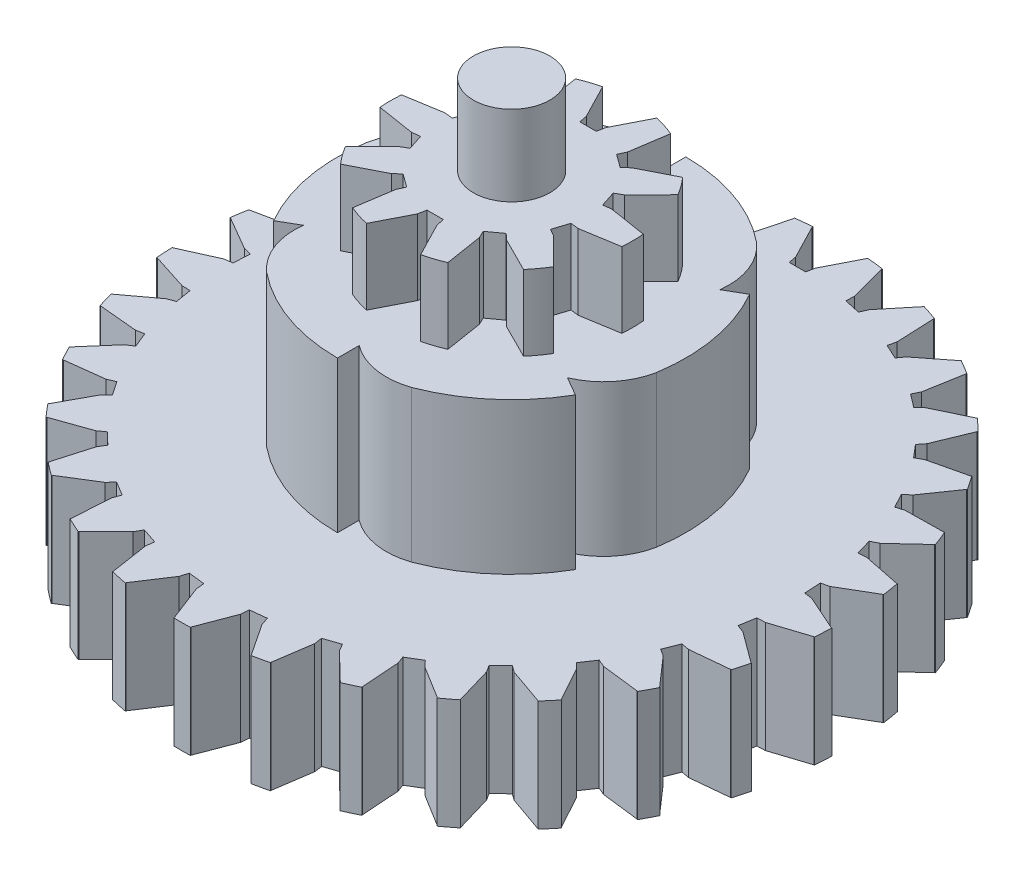
SolidWorks part; units mm, degrees
material "Gray Cast Iron"
ref_plane "Front Plane" through (0, 0, 0) normal (0, 0, 1) x (1, 0, 0)
ref_plane "Top Plane" through (0, 0, 0) normal (0, 1, 0) x (1, 0, 0)
ref_plane "Right Plane" through (0, 0, 0) normal (1, 0, 0) x (0, 0, -1)
sketch "Sketch1" plane through (0, 0, 0) normal (0, 1, 0) x (1, 0, 0)
  circle A0 centre (-83.1207, 52.7325) radius 4.5085
extrude "Boss-Extrude1" add sketch "Sketch1" along normal blind 2.794
sketch "Sketch2" plane through (0, 2.794, 0) normal (0, 1, 0) x (1, 0, 0)
  circle A0 centre (-83.1207, 52.7325) radius 1.4224
extrude "Boss-Extrude2" add sketch "Sketch2" along normal blind 2.9845
sketch "Sketch3" plane through (0, 2.794, 0) normal (0, 1, 0) x (1, 0, 0)
  line L0 (-83.1207, 55.5745) -> (-82.8159, 55.5745)
  line L1 (-83.1207, 55.5745) -> (-83.4255, 55.5745)
  line L2 (-83.4255, 55.5745) -> (-83.4853, 55.8734)
  line L3 (-82.8159, 55.5745) -> (-82.7574, 55.8745)
  line L4 (-82.7574, 55.8745) -> (-82.1099, 57.1432)
  line L5 (-83.4853, 55.8734) -> (-84.1407, 57.1427)
  line L6 (-83.1207, 52.7325) -> (-83.1207, 57.241)
  line L7 (-84.1407, 57.1427) -> (-84.2034, 57.9061)
  line L8 (-84.2034, 57.9061) -> (-82.0598, 57.9061)
  line L9 (-82.0598, 57.9061) -> (-82.1099, 57.1432)
  line L10 (-81.5695, 55.4878) -> (-81.3537, 56.8999)
  line L11 (-79.2215, 56.2944) -> (-79.7104, 55.7067)
  line L12 (-80.9799, 55.0609) -> (-79.7104, 55.7067)
  line L13 (-81.2036, 54.8526) -> (-80.9799, 55.0609)
  line L14 (-81.4502, 55.0317) -> (-81.2036, 54.8526)
  line L15 (-81.4502, 55.0317) -> (-81.6968, 55.2109)
  line L16 (-81.6968, 55.2109) -> (-81.5695, 55.4878)
  line L17 (-81.3537, 56.8999) -> (-80.9557, 57.5544)
  line L18 (-80.9557, 57.5544) -> (-79.2215, 56.2944)
  line L19 (-80.2462, 54.0498) -> (-79.2416, 55.0654)
  line L20 (-77.8725, 53.3223) -> (-78.6135, 53.1341)
  line L21 (-80.0202, 53.3579) -> (-78.6135, 53.1341)
  line L22 (-80.3236, 53.3208) -> (-80.0202, 53.3579)
  line L23 (-80.4178, 53.6107) -> (-80.3236, 53.3208)
  line L24 (-80.4178, 53.6107) -> (-80.512, 53.9006)
  line L25 (-80.512, 53.9006) -> (-80.2462, 54.0498)
  line L26 (-79.2416, 55.0654) -> (-78.5349, 55.3609)
  line L27 (-78.5349, 55.3609) -> (-77.8725, 53.3223)
  line L28 (-80.0209, 52.1086) -> (-78.6112, 52.3397)
  line L29 (-78.5282, 50.1248) -> (-79.2382, 50.4081)
  line L30 (-80.2447, 51.416) -> (-79.2382, 50.4081)
  line L31 (-80.512, 51.5644) -> (-80.2447, 51.416)
  line L32 (-80.4178, 51.8543) -> (-80.512, 51.5644)
  line L33 (-80.4178, 51.8543) -> (-80.3236, 52.1441)
  line L34 (-80.3236, 52.1441) -> (-80.0209, 52.1086)
  line L35 (-78.6112, 52.3397) -> (-77.8658, 52.1635)
  line L36 (-77.8658, 52.1635) -> (-78.5282, 50.1248)
  line L37 (-80.9796, 50.4058) -> (-79.7033, 49.7641)
  line L38 (-80.938, 47.9234) -> (-81.3459, 48.57)
  line L39 (-81.5678, 49.977) -> (-81.3459, 48.57)
  line L40 (-81.6968, 50.2541) -> (-81.5678, 49.977)
  line L41 (-81.4502, 50.4333) -> (-81.6968, 50.2541)
  line L42 (-81.4502, 50.4333) -> (-81.2036, 50.6124)
  line L43 (-81.2036, 50.6124) -> (-80.9796, 50.4058)
  line L44 (-79.7033, 49.7641) -> (-79.2038, 49.1834)
  line L45 (-79.2038, 49.1834) -> (-80.938, 47.9234)
  line L46 (-82.7561, 49.5916) -> (-82.1007, 48.3223)
  line L47 (-84.1816, 47.5589) -> (-84.1315, 48.3217)
  line L48 (-83.484, 49.5904) -> (-84.1315, 48.3217)
  line L49 (-83.4255, 49.8905) -> (-83.484, 49.5904)
  line L50 (-83.1207, 49.8905) -> (-83.4255, 49.8905)
  line L51 (-83.1207, 49.8905) -> (-82.8159, 49.8905)
  line L52 (-82.8159, 49.8905) -> (-82.7561, 49.5916)
  line L53 (-82.1007, 48.3223) -> (-82.038, 47.5589)
  line L54 (-82.038, 47.5589) -> (-84.1816, 47.5589)
  line L55 (-84.6719, 49.9772) -> (-84.8877, 48.5651)
  line L56 (-87.0199, 49.1705) -> (-86.5311, 49.7583)
  line L57 (-85.2615, 50.4041) -> (-86.5311, 49.7583)
  line L58 (-85.0378, 50.6124) -> (-85.2615, 50.4041)
  line L59 (-84.7912, 50.4333) -> (-85.0378, 50.6124)
  line L60 (-84.7912, 50.4333) -> (-84.5446, 50.2541)
  line L61 (-84.5446, 50.2541) -> (-84.6719, 49.9772)
  line L62 (-84.8877, 48.5651) -> (-85.2857, 47.9106)
  line L63 (-85.2857, 47.9106) -> (-87.0199, 49.1705)
  line L64 (-85.9952, 51.4152) -> (-86.9998, 50.3996)
  line L65 (-88.3689, 52.1427) -> (-87.6279, 52.3309)
  line L66 (-86.2212, 52.1071) -> (-87.6279, 52.3309)
  line L67 (-85.9178, 52.1441) -> (-86.2212, 52.1071)
  line L68 (-85.8236, 51.8543) -> (-85.9178, 52.1441)
  line L69 (-85.8236, 51.8543) -> (-85.7294, 51.5644)
  line L70 (-85.7294, 51.5644) -> (-85.9952, 51.4152)
  line L71 (-86.9998, 50.3996) -> (-87.7065, 50.104)
  line L72 (-87.7065, 50.104) -> (-88.3689, 52.1427)
  line L73 (-86.2205, 53.3563) -> (-87.6302, 53.1252)
  line L74 (-87.7132, 55.3402) -> (-87.0032, 55.0568)
  line L75 (-85.9967, 54.049) -> (-87.0032, 55.0568)
  line L76 (-85.7294, 53.9006) -> (-85.9967, 54.049)
  line L77 (-85.8236, 53.6107) -> (-85.7294, 53.9006)
  line L78 (-85.8236, 53.6107) -> (-85.9178, 53.3208)
  line L79 (-85.9178, 53.3208) -> (-86.2205, 53.3563)
  line L80 (-87.6302, 53.1252) -> (-88.3756, 53.3015)
  line L81 (-88.3756, 53.3015) -> (-87.7132, 55.3402)
  line L82 (-85.2618, 55.0592) -> (-86.5381, 55.7009)
  line L83 (-85.3034, 57.5416) -> (-84.8955, 56.895)
  line L84 (-84.6736, 55.488) -> (-84.8955, 56.895)
  line L85 (-84.5446, 55.2109) -> (-84.6736, 55.488)
  line L86 (-84.7912, 55.0317) -> (-84.5446, 55.2109)
  line L87 (-84.7912, 55.0317) -> (-85.0378, 54.8526)
  line L88 (-85.0378, 54.8526) -> (-85.2618, 55.0592)
  line L89 (-86.5381, 55.7009) -> (-87.0376, 56.2816)
  line L90 (-87.0376, 56.2816) -> (-85.3034, 57.5416)
  line L91 (-83.1207, 52.7325) -> (-83.1207, 55.5745) construction
  circle A0 centre (-83.1207, 52.7325) radius 4.5085 construction
  circle M11 centre (-83.1207, 52.7325) radius 4.5085
  dimension "D1" = 10
  dimension "D2" = 2.842
extrude "Cut-Extrude1" cut sketch "Sketch3" against normal through all contours L88 L87 L86 L85 L84 L82 M11 | L6 L0 L3 L4 M11 | L1 L6 L5 L2 M11 | L16 L15 L14 L13 L12 L10 M11 | L25 L24 L23 L22 L21 L19 M11 | L34 L33 L32 L31 L30 L28 M11 | L43 L42 L41 L40 L39 L37 M11 | L52 L51 L50 L49 L48 L46 M11 | L61 L60 L59 L58 L57 L55 M11 | L70 L69 L68 L67 L66 L64 M11 | L79 L78 L77 L76 L75 L73 M11
sketch "Sketch4" plane through (0, 0, 0) normal (0, -1, 0) x (1, 0, 0)
  circle A0 centre (-83.1207, -52.7325) radius 6.477
extrude "Boss-Extrude3" add sketch "Sketch4" along normal blind 5.6261
sketch "Sketch5" plane through (0, 0, 0) normal (0, 1, 0) x (1, 0, 0)
  line L0 (-83.1207, 58.4015) -> (-83.1207, 59.2095)
  line L6 (-78.2112, 55.567) -> (-77.5115, 55.971)
  line L7 (-78.2112, 49.898) -> (-77.5115, 49.494)
  line L8 (-83.1207, 47.0635) -> (-83.1207, 46.2555)
  line L9 (-88.0302, 49.898) -> (-88.7299, 49.494)
  line L10 (-88.0302, 55.567) -> (-88.7299, 55.971)
  line L11 (-83.1207, 52.7325) -> (-84.6382, 56.3955) construction
  circle A0 centre (-83.1207, 52.7325) radius 6.477 construction
  arc A2 (-83.1207, 58.4015) -> (-85.4488, 58.7766) centre (-84.6382, 56.3955) ccw
  arc A3 (-85.4488, 58.7766) -> (-83.1207, 59.2095) centre (-83.1207, 52.7325) cw
  arc A14 (-79.0504, 57.7708) -> (-77.5115, 55.971) centre (-83.1207, 52.7325) cw
  arc A15 (-78.2112, 55.567) -> (-79.0504, 57.7708) centre (-80.7072, 55.8782) ccw
  arc A16 (-76.7223, 51.7267) -> (-77.5115, 49.494) centre (-83.1207, 52.7325) cw
  arc A17 (-78.2112, 49.898) -> (-76.7223, 51.7267) centre (-79.1897, 52.2152) ccw
  arc A18 (-80.7926, 46.6884) -> (-83.1207, 46.2555) centre (-83.1207, 52.7325) cw
  arc A19 (-83.1207, 47.0635) -> (-80.7926, 46.6884) centre (-81.6032, 49.0695) ccw
  arc A20 (-87.191, 47.6942) -> (-88.7299, 49.494) centre (-83.1207, 52.7325) cw
  arc A21 (-88.0302, 49.898) -> (-87.191, 47.6942) centre (-85.5342, 49.5868) ccw
  arc A22 (-89.5191, 53.7383) -> (-88.7299, 55.971) centre (-83.1207, 52.7325) cw
  arc A23 (-88.0302, 55.567) -> (-89.5191, 53.7383) centre (-87.0517, 53.2498) ccw
  dimension "D1" = 6
  dimension "D2" = 3.9649
extrude "Cut-Extrude2" cut sketch "Sketch5" against normal through all contours L0 A3 A2 | A23 A22 L10 | A21 A20 L9 | A19 A18 L8 | A17 A16 L7 | A15 A14 L6
sketch "Sketch6" plane through (0, -5.6261, 0) normal (0, -1, 0) x (1, 0, 0)
  circle A0 centre (-83.1207, -52.7325) radius 12.2619
extrude "Boss-Extrude4" add sketch "Sketch6" along normal blind 4.1275 contours A0
sketch "Sketch7" plane through (0, -9.7536, 0) normal (0, -1, 0) x (1, 0, 0)
  circle A0 centre (-83.1207, -52.7325) radius 1.4224
extrude "Boss-Extrude5" add sketch "Sketch7" along normal blind 3.302 contours A0
ref_plane "Plane1" through (0, 0, -40.4622) normal (0, 0, 1) x (1, 0, 0)
sketch "Sketch11" plane through (0, -5.6261, 0) normal (0, 1, 0) x (1, 0, 0)
  line L0 (-83.1207, 52.7325) -> (-83.1207, 64.9943)
  line L1 (-83.1207, 63.3604) -> (-82.8159, 63.3604)
  line L2 (-83.1207, 63.3604) -> (-83.4255, 63.3604)
  line L3 (-83.4255, 63.3604) -> (-83.4853, 63.6593)
  line L4 (-82.8159, 63.3604) -> (-82.7574, 63.6604)
  line L5 (-82.7574, 63.6604) -> (-82.1099, 64.9291)
  line L6 (-83.4853, 63.6593) -> (-84.1407, 64.9286)
  line L7 (-84.1407, 64.9286) -> (-84.2034, 65.692)
  line L9 (-82.0598, 65.692) -> (-82.1099, 64.9291)
  line L10 (-84.2034, 65.692) -> (-82.0598, 65.692)
  circle A0 centre (-83.1207, 52.7325) radius 12.2619 construction
extrude "Cut-Extrude4" cut sketch "Sketch11" against normal through all and the other way through all
pattern_circular "CirPattern3" count 29 over 360 about axis through (-83.1207, 0, -52.7325) along (0, 1, 0) of "Cut-Extrude4"
